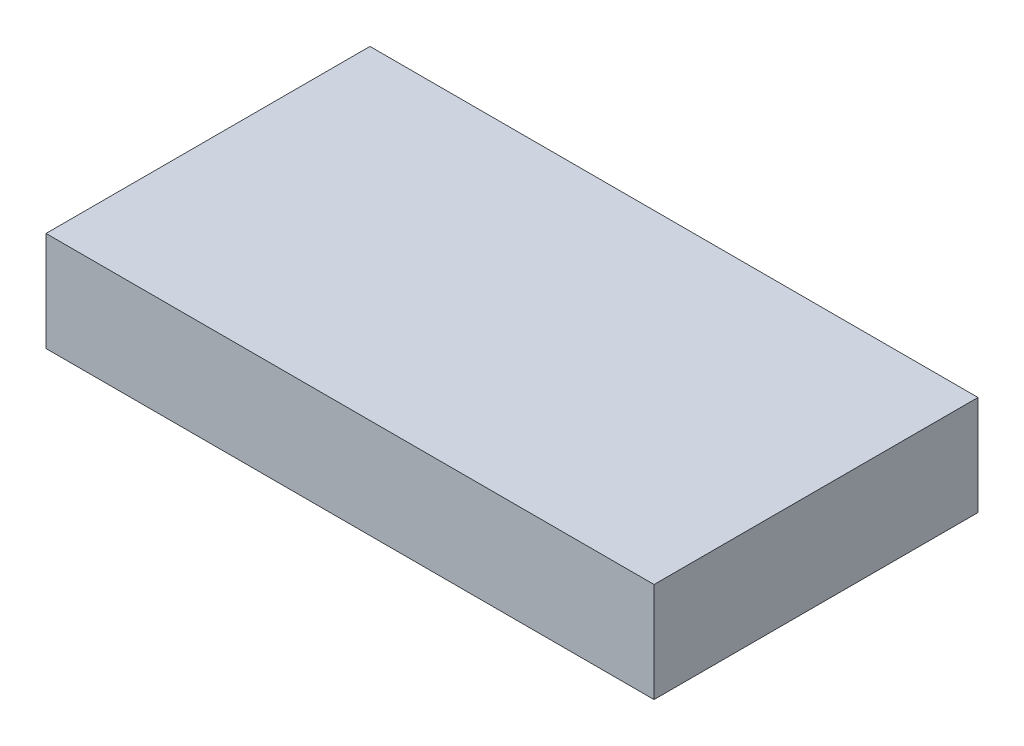
SolidWorks part; units mm, degrees
ref_plane "Front Plane" through (0, 0, 0) normal (0, 0, 1) x (1, 0, 0)
ref_plane "Top Plane" through (0, 0, 0) normal (0, 1, 0) x (1, 0, 0)
ref_plane "Right Plane" through (0, 0, 0) normal (1, 0, 0) x (0, 0, -1)
sketch "Sketch1" plane through (0, 0, 0) normal (0, 1, 0) x (1, 0, 0)
  line L1 (0, -0.5) -> (12.2, -0.5)
  line L2 (0, -0.5) -> (0, 6)
  line L3 (0, 6) -> (12.2, 6)
  line L4 (12.2, -0.5) -> (12.2, 6)
  dimension "D1" = 12.2
  dimension "D2" = 6.5
  dimension "D3" = 0.5
extrude "Boss-Extrude1" add sketch "Sketch1" along normal blind 2
